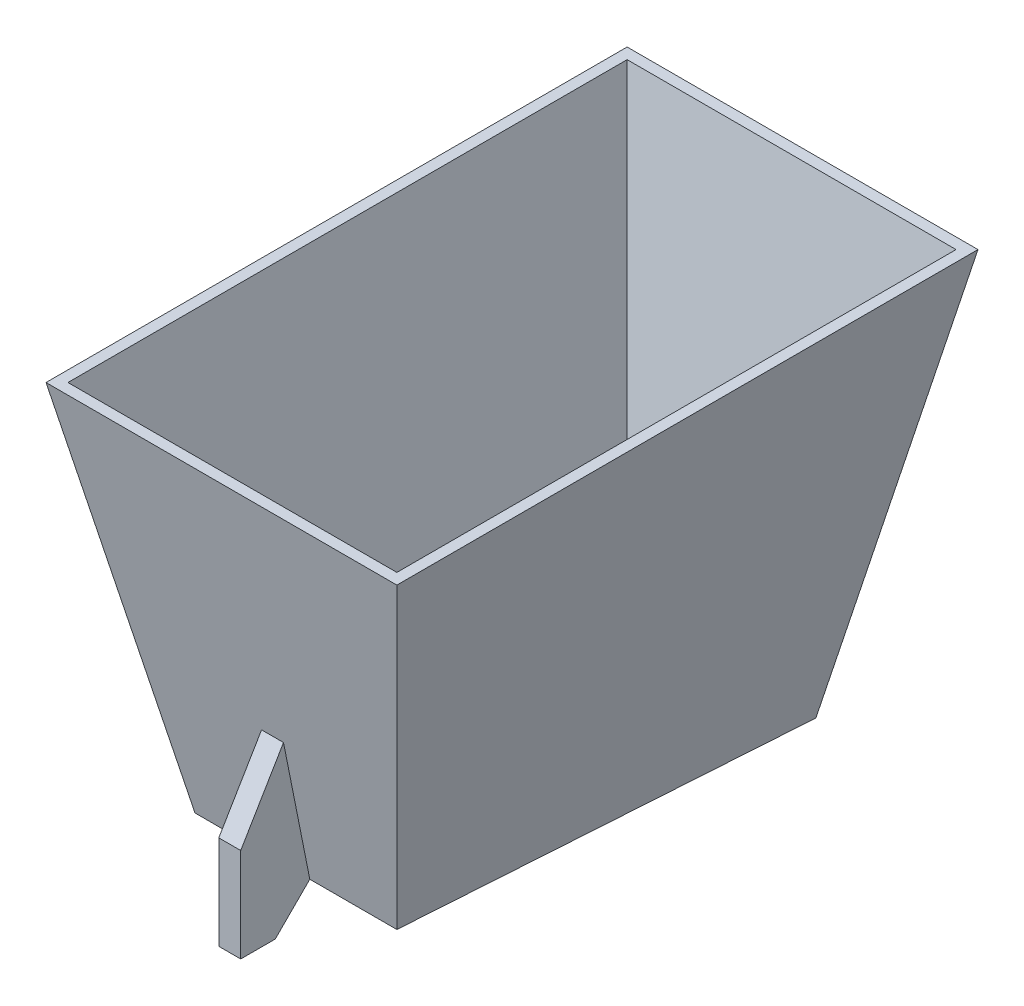
SolidWorks part; units mm, degrees
ref_plane "Front" through (0, 0, 0) normal (0, 0, 1) x (1, 0, 0)
ref_plane "Top" through (0, 0, 0) normal (0, 1, 0) x (1, 0, 0)
ref_plane "Right" through (0, 0, 0) normal (1, 0, 0) x (0, 0, -1)
sketch "Sketch1" plane through (0, 0, 0) normal (0, 1, 0) x (1, 0, 0)
  line L1 (-284.8524, 134.0482) -> (-81.6524, 134.0482)
  line L2 (-284.8524, 134.0482) -> (-284.8524, -202.5018)
  line L3 (-284.8524, -202.5018) -> (-81.6524, -202.5018)
  line L4 (-81.6524, 134.0482) -> (-81.6524, -202.5018)
  dimension "D1" = 336.55
  dimension "D2" = 203.2
extrude "Boss-Extrude4" add sketch "Sketch1" along normal blind 254 draft 11.3
sketch "Sketch3" plane through (0, 0, 0) normal (0, -1, 0) x (1, 0, 0)
  line L14 (-278.5024, 196.1518) -> (-278.5024, -127.6982)
  line L15 (-278.5024, -127.6982) -> (-88.0024, -127.6982)
  line L16 (-88.0024, -127.6982) -> (-88.0024, 196.1518)
  line L17 (-88.0024, 196.1518) -> (-278.5024, 196.1518)
  line L18 (-278.5024, 196.1518) -> (-278.5024, -127.6982)
  line L19 (-278.5024, -127.6982) -> (-88.0024, -127.6982)
  line L20 (-88.0024, -127.6982) -> (-88.0024, 196.1518)
  line L21 (-88.0024, 196.1518) -> (-278.5024, 196.1518)
  dimension "D1" = 6.35
extrude "Cut-Extrude1" cut sketch "Sketch3" against normal blind 247.65 draft 11.25
ref_plane "Plane3" through (-294, 0, 0) normal (1, 0, 0) x (0, 0, -1)
sketch "Sketch15" plane through (-294, 0, 0) normal (1, 0, 0) x (0, 0, -1)
  line L0 (83.294, 254) -> (-151.7476, 254)
  line L1 (-151.7476, 254) -> (-202.5018, 0) construction
  line L2 (-151.7476, 254) -> (-159.3608, 215.9)
  line L3 (-159.3608, 215.9) -> (87.1005, 234.95)
  line L4 (83.294, 254) -> (134.0482, 0) construction
  line L5 (87.1005, 234.95) -> (83.294, 254)
  dimension "D1" = 19.05
  dimension "D2" = 38.1
extrude "Cut-Extrude13" cut sketch "Sketch15" along normal blind 254
sketch "Sketch21" plane through (-294, 0, 0) normal (1, 0, 0) x (0, 0, -1)
  line L0 (-159.3608, 215.9) -> (-179.3608, 235.9)
  line L1 (-179.3608, 235.9) -> (-179.3608, 215.9)
  line L2 (-179.3608, 215.9) -> (-159.3608, 215.9)
  line L3 (-174.587, 139.7) -> (-199.3608, 181.4737)
  line L4 (-199.3608, 181.4737) -> (-199.3608, 235.9)
  line L5 (-199.3608, 235.9) -> (-179.3608, 235.9)
  line L6 (-159.3608, 215.9) -> (-202.5018, 0) construction
  line L7 (-174.587, 139.7) -> (-159.3608, 215.9)
  dimension "D1" = 20
  dimension "D2" = 20
  dimension "D3" = 20
  dimension "D4" = 76.2
extrude "Boss-Extrude6" add sketch "Sketch21" along normal blind 12.7 from offset 102.7176 contours L3 L7 L2 L1 L5 L4 | L1 L2 L0
sketch "Sketch22" plane through (0, 226.8623, 17.5351) normal (0, 0.997, 0.0771) x (1, 0, 0)
  line L0 (-237.9047, 104.9477) -> (-241.7113, -142.2487)
  line L1 (-241.7113, -142.2487) -> (-124.7934, -142.2487)
  line L2 (-124.7934, -142.2487) -> (-128.6, 104.9477)
  line L3 (-128.6, 104.9477) -> (-237.9047, 104.9477)
extrude "Boss-Extrude7" add sketch "Sketch22" against normal blind 6.35
move or copy body "Body-Move/Copy1" bodies to move or copy 121 copy no rotation origin (0, 117.95, 34.2268) rotation axis (1, 0, 0) rotation angle 180
move or copy body "Body-Move/Copy2" bodies to move or copy 122 copy no rotation origin (-183.2524, 0, 34.2268) rotation axis (0, 1, 0) rotation angle 180
